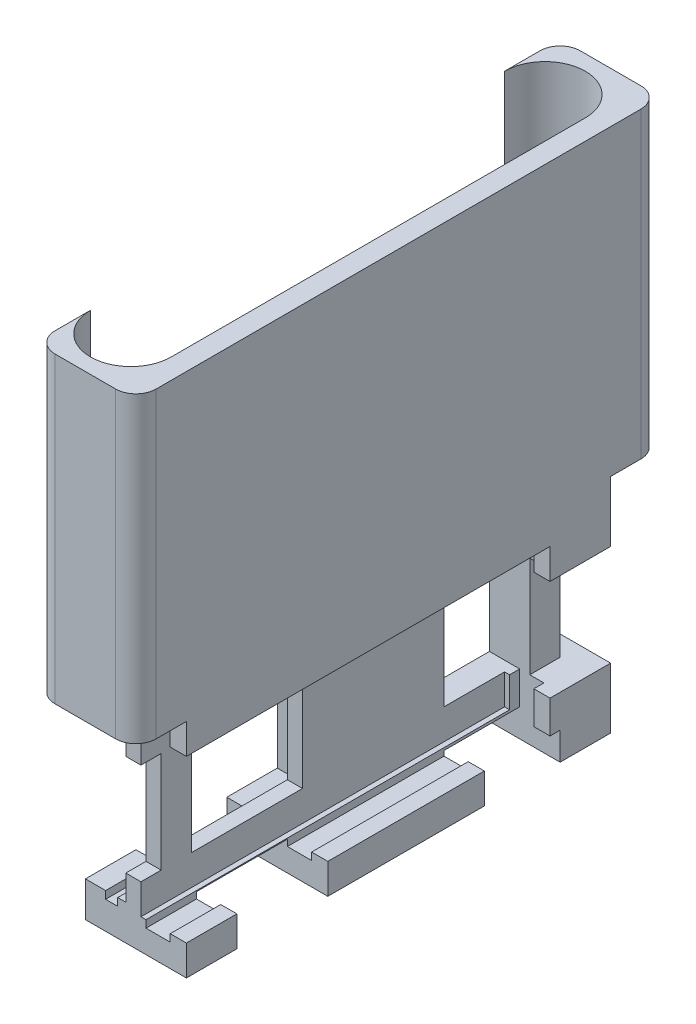
SolidWorks part; units mm, degrees
ref_plane "Front Plane" through (0, 0, 0) normal (0, 0, 1) x (1, 0, 0)
ref_plane "Top Plane" through (0, 0, 0) normal (0, 1, 0) x (1, 0, 0)
ref_plane "Right Plane" through (0, 0, 0) normal (1, 0, 0) x (0, 0, -1)
sketch "Sketch1" plane through (0, 0, 0) normal (0, 0, 1) x (1, 0, 0)
  line L1 (-5, -11) -> (5, -11)
  line L2 (-5, -11) -> (-5, 11)
  line L3 (-5, 11) -> (5, 11)
  line L4 (5, -11) -> (5, 11)
  line L5 (-5, -11) -> (5, 11) construction
  line L6 (-5, 11) -> (5, -11) construction
  point P0 (0, 0)
  dimension "D1" = 22
  dimension "D2" = 10
extrude "Boss-Extrude1" add sketch "Sketch1" along normal blind 42
sketch "Sketch2" plane through (0, 0, 42) normal (0, 0, 1) x (1, 0, 0)
  line L1 (5, -8) -> (0.5, -8)
  line L2 (5, -8) -> (5, 8)
  line L3 (5, 8) -> (0.5, 8)
  line L4 (0.5, -8) -> (0.5, 8)
  line L5 (5, -8) -> (0.5, 8) construction
  line L6 (5, 8) -> (0.5, -8) construction
  line L7 (5, -11) -> (5, 11) construction
  line L8 (-5, 11) -> (-5, -11) construction
  point P0 (2.75, 0)
  point P5 (-5, 0)
  dimension "D1" = 4.5
  dimension "D2" = 0
  dimension "D3" = 16
  dimension "D4" = 0
extrude "Cut-Extrude1" cut sketch "Sketch2" against normal blind 36
sketch "Sketch4" plane through (0, 0, 42) normal (0, 0, 1) x (1, 0, 0)
  line L0 (0.5, 8) -> (0.5, -8) construction
  line L1 (1, -8.7267) -> (3.4, -8.7267)
  line L2 (1, -8.7267) -> (1, 9.4733)
  line L3 (1, 9.4733) -> (3.4, 9.4733)
  line L4 (3.4, -8.7267) -> (3.4, 9.4733)
  line L5 (1, -8.7267) -> (3.4, 9.4733) construction
  line L6 (1, 9.4733) -> (3.4, -8.7267) construction
  point P0 (2.2, 0.3733)
  dimension "D1" = 18.2
  dimension "D2" = 2.4
  dimension "D3" = 0.5
extrude "Cut-Extrude3" cut sketch "Sketch4" against normal blind 37
sketch "Sketch5" plane through (0, 0, 42) normal (0, 0, 1) x (1, 0, 0)
  line L0 (-5, 11) -> (-5, -11) construction
  line L1 (-5, -7.5) -> (-1, -7.5)
  line L2 (-5, -7.5) -> (-5, 7.5)
  line L3 (-5, 7.5) -> (-1, 7.5)
  line L4 (-1, -7.5) -> (-1, 7.5)
  line L5 (-5, -7.5) -> (-1, 7.5) construction
  line L6 (-5, 7.5) -> (-1, -7.5) construction
  point P0 (-3, 0)
  dimension "D1" = 4
  dimension "D2" = 0
  dimension "D3" = 15
  dimension "D4" = 0
extrude "Cut-Extrude4" cut sketch "Sketch5" against normal blind 19
sketch "Sketch6" plane through (0, 0, 42) normal (0, 0, 1) x (1, 0, 0)
  line L0 (-5, 11) -> (-5, 7.5) construction
  line L1 (-3, -8.25) -> (-1.8, -8.25)
  line L2 (-3, -8.25) -> (-3, 8.25)
  line L3 (-3, 8.25) -> (-1.8, 8.25)
  line L4 (-1.8, -8.25) -> (-1.8, 8.25)
  line L5 (-3, -8.25) -> (-1.8, 8.25) construction
  line L6 (-3, 8.25) -> (-1.8, -8.25) construction
  point P0 (-2.4, 0)
  dimension "D1" = 1.2
  dimension "D2" = 2
  dimension "D3" = 16.5
  dimension "D4" = 0
extrude "Cut-Extrude5" cut sketch "Sketch6" against normal blind 20.5
sketch "Sketch8" plane through (0, 0, 0) normal (0, 0, -1) x (-1, 0, 0)
  line L0 (5, 11) -> (5, -11) construction
  line L1 (2, -7.25) -> (5, -7.25)
  line L2 (2, -7.25) -> (2, 7.25)
  line L3 (2, 7.25) -> (5, 7.25)
  line L4 (5, -7.25) -> (5, 7.25)
  line L5 (2, -7.25) -> (5, 7.25) construction
  line L6 (2, 7.25) -> (5, -7.25) construction
  point P0 (3.5, 0)
  dimension "D1" = 3
  dimension "D2" = 0
  dimension "D3" = 14.5
  dimension "D4" = 0
extrude "Cut-Extrude6" cut sketch "Sketch8" against normal blind 15.5
sketch "Sketch9" plane through (0, 0, 0) normal (0, 0, -1) x (-1, 0, 0)
  line L0 (2, 7.25) -> (2, -7.25) construction
  line L1 (3.7, -8.25) -> (2.5, -8.25)
  line L2 (3.7, -8.25) -> (3.7, 8.25)
  line L3 (3.7, 8.25) -> (2.5, 8.25)
  line L4 (2.5, -8.25) -> (2.5, 8.25)
  line L5 (3.7, -8.25) -> (2.5, 8.25) construction
  line L6 (3.7, 8.25) -> (2.5, -8.25) construction
  point P0 (3.1, 0)
  dimension "D1" = 0.5
  dimension "D2" = 16.5
  dimension "D3" = 0
  dimension "D4" = 1.2
extrude "Cut-Extrude7" cut sketch "Sketch9" against normal blind 16.5
sketch "Sketch10" plane through (-5, 0, 0) normal (-1, 0, 0) x (0, 0, 1)
  line L1 (2, -8) -> (14, -8)
  line L2 (2, -8) -> (2, 8)
  line L3 (2, 8) -> (14, 8)
  line L4 (14, -8) -> (14, 8)
  line L5 (2, -8) -> (14, 8) construction
  line L6 (2, 8) -> (14, -8) construction
  line L7 (0, 11) -> (0, 7.25) construction
  line L8 (15.5, -7.25) -> (15.5, 7.25) construction
  point P0 (8, 0)
  point P7 (15.5, 0)
  dimension "D1" = 16
  dimension "D2" = 12
  dimension "D3" = 2
  dimension "D4" = 0
extrude "Cut-Extrude8" cut sketch "Sketch10" against normal blind 2.5
sketch "Sketch12" plane through (-5, 0, 0) normal (-1, 0, 0) x (0, 0, 1)
  line L0 (42, -11) -> (0, -11) construction
  line L1 (37, -11) -> (28, -11)
  line L2 (37, -11) -> (37, -8.1)
  line L3 (37, -8.1) -> (28, -8.1)
  line L4 (28, -11) -> (28, -8.1)
  line L5 (42, -7.5) -> (42, -11) construction
  line L6 (12.5, -11) -> (5, -11)
  line L7 (12.5, -11) -> (12.5, -8.25)
  line L8 (12.5, -8.25) -> (5, -8.25)
  line L9 (5, -11) -> (5, -8.25)
  line L10 (23, 7.5) -> (23, -7.5) construction
  line L11 (0, -7.25) -> (0, -11) construction
  line L12 (15.5, -7.25) -> (15.5, 7.25) construction
  dimension "D1" = 2.9
  dimension "D2" = 2.75
  dimension "D3" = 5
  dimension "D4" = 5
  dimension "D5" = 5
  dimension "D6" = 3
extrude "Cut-Extrude11" cut sketch "Sketch12" against normal blind 10
sketch "Sketch13" plane through (-5, 0, 0) normal (-1, 0, 0) x (0, 0, 1)
  line L0 (23, -7.5) -> (42, -7.5) construction
  line L1 (37, -8.1) -> (28, -8.1)
  line L2 (37, -8.1) -> (37, -7.5)
  line L3 (37, -7.5) -> (28, -7.5)
  line L4 (28, -8.1) -> (28, -7.5)
  line L5 (2, -8) -> (14, -8) construction
  line L6 (12.5, -8.25) -> (5, -8.25)
  line L7 (12.5, -8.25) -> (12.5, -8)
  line L8 (12.5, -8) -> (5, -8)
  line L9 (5, -8.25) -> (5, -8)
extrude "Cut-Extrude12" cut sketch "Sketch13" against normal up to next
sketch "Sketch14" plane through (5, 0, 0) normal (1, 0, 0) x (0, 0, -1)
  line L0 (-6, -8) -> (-42, -8) construction
  line L1 (-37, -8.1) -> (-28, -8.1)
  line L2 (-37, -8.1) -> (-37, -8)
  line L3 (-37, -8) -> (-28, -8)
  line L4 (-28, -8.1) -> (-28, -8)
  line L6 (-12.5, -8.25) -> (-6, -8.25)
  line L7 (-12.5, -8.25) -> (-12.5, -8)
  line L8 (-12.5, -8) -> (-6, -8)
  line L9 (-6, -8.25) -> (-6, -8)
extrude "Cut-Extrude13" cut sketch "Sketch14" against normal up to next
sketch "Sketch15" plane through (-1, 0, 0) normal (-1, 0, 0) x (0, 0, 1)
  line L0 (42, -7.5) -> (42, 7.5) construction
  line L1 (40, 5) -> (42, 5)
  line L2 (40, 5) -> (40, -5)
  line L3 (40, -5) -> (42, -5)
  line L4 (42, 5) -> (42, -5)
  line L5 (40, 5) -> (42, -5) construction
  line L6 (40, -5) -> (42, 5) construction
  line L7 (26, 5) -> (37, 5)
  line L8 (26, 5) -> (26, -5)
  line L9 (26, -5) -> (37, -5)
  line L10 (37, 5) -> (37, -5)
  line L11 (26, 5) -> (37, -5) construction
  line L12 (26, -5) -> (37, 5) construction
  point P0 (41, 0)
  point P5 (31.5, 0)
  point P12 (42, 0)
  point P13 (42, 0)
  dimension "D1" = 10
  dimension "D2" = 10
  dimension "D3" = 0
  dimension "D4" = 0
  dimension "D5" = 0
  dimension "D6" = 2
  dimension "D7" = 3
  dimension "D8" = 11
extrude "Cut-Extrude14" cut sketch "Sketch15" against normal through all
sketch "Sketch16" plane through (-2, 0, 0) normal (-1, 0, 0) x (0, 0, 1)
  line L0 (0, 7.25) -> (0, -7.25) construction
  line L1 (2, 5) -> (0, 5)
  line L2 (2, 5) -> (2, -5)
  line L3 (2, -5) -> (0, -5)
  line L4 (0, 5) -> (0, -5)
  line L5 (2, 5) -> (0, -5) construction
  line L6 (2, -5) -> (0, 5) construction
  line L7 (15.5, 7.25) -> (15.5, -7.25) construction
  line L8 (12, 5) -> (5, 5)
  line L9 (12, 5) -> (12, -5)
  line L10 (12, -5) -> (5, -5)
  line L11 (5, 5) -> (5, -5)
  line L12 (12, 5) -> (5, -5) construction
  line L13 (12, -5) -> (5, 5) construction
  point P0 (1, 0)
  point P7 (8.5, 0)
  point P12 (15.5, 0)
  dimension "D1" = 10
  dimension "D2" = 2
  dimension "D3" = 3
  dimension "D4" = 7
  dimension "D5" = 10
  dimension "D6" = 0
  dimension "D7" = 0
extrude "Cut-Extrude15" cut sketch "Sketch16" against normal blind 10
sketch "Sketch17" plane through (0, 0, 2) normal (0, 0, -1) x (-1, 0, 0)
  line L0 (-5, 5) -> (2, 5) construction
  line L1 (-5, -5) -> (-2, -5)
  line L2 (-5, -5) -> (-5, 5)
  line L3 (-5, 5) -> (-2, 5)
  line L4 (-2, -5) -> (-2, 5)
  dimension "D1" = 3
extrude "Cut-Extrude16" cut sketch "Sketch17" against normal blind 10
sketch "Sketch18" plane through (0, 11, 0) normal (0, 1, 0) x (1, 0, 0)
  line L0 (5, -42) -> (5, 0) construction
  line L1 (-5, 5) -> (5, 5)
  line L2 (-5, 5) -> (-5, -47)
  line L3 (-5, -47) -> (5, -47)
  line L4 (5, 5) -> (5, -47)
  line L5 (-5, 5) -> (5, -47) construction
  line L6 (-5, -47) -> (5, 5) construction
  line L7 (-5, -42) -> (-5, 0) construction
  point P0 (0, -21)
  point P5 (5, -21)
  point P11 (-5, -21)
  dimension "D1" = 10
  dimension "D2" = 52
  dimension "D3" = 5
  dimension "D4" = 0
extrude "Boss-Extrude3" add sketch "Sketch18" along normal blind 30
sketch "Sketch21" plane through (0, 8, 0) normal (0, -1, 0) x (1, 0, 0)
  line L0 (-5, 14) -> (-5, 2) construction
  line L1 (-5, 12) -> (-3.7, 12)
  line L2 (-5, 12) -> (-5, 6)
  line L3 (-5, 6) -> (-3.7, 6)
  line L4 (-3.7, 12) -> (-3.7, 6)
  line L5 (-3.7, 14) -> (-3.7, 2) construction
  line L6 (-3.7, 14) -> (-5, 14) construction
  line L7 (-3.7, 2) -> (-5, 2) construction
  dimension "D1" = 2
  dimension "D2" = 4
extrude "Cut-Extrude18" cut sketch "Sketch21" against normal blind 28
fillet "Fillet1" radius 2 4 edges at (5, 26, -5) (-5, 26, -5) (5, 26, 47) (-5, 26, 47)
fillet "Fillet3" radius 1 1 edges at (-3.7, 8.25, 9)
sketch "Sketch22" plane through (0, 41, 0) normal (0, 1, 0) x (1, 0, 0)
  line L0 (-1, -41.5) -> (-1, -0.5) construction
  line L1 (-5, -41.5) -> (-5, -0.5)
  line L2 (3, -41.5) -> (3, -0.5)
  line L3 (-5, 3) -> (-5, -45) construction
  line L4 (5, -45) -> (5, 3) construction
  arc A0 (-5, -41.5) -> (3, -41.5) centre (-1, -41.5) ccw
  arc A1 (3, -0.5) -> (-5, -0.5) centre (-1, -0.5) ccw
  point P2 (-1, -21)
  point P9 (5, -21)
  dimension "D1" = 8
  dimension "D2" = 41
  dimension "D3" = 0
  dimension "D4" = 0
extrude "Cut-Extrude19" cut sketch "Sketch22" against normal blind 28
fillet "Fillet4" radius 2 1 edges at (-3.7, 13, 9)
